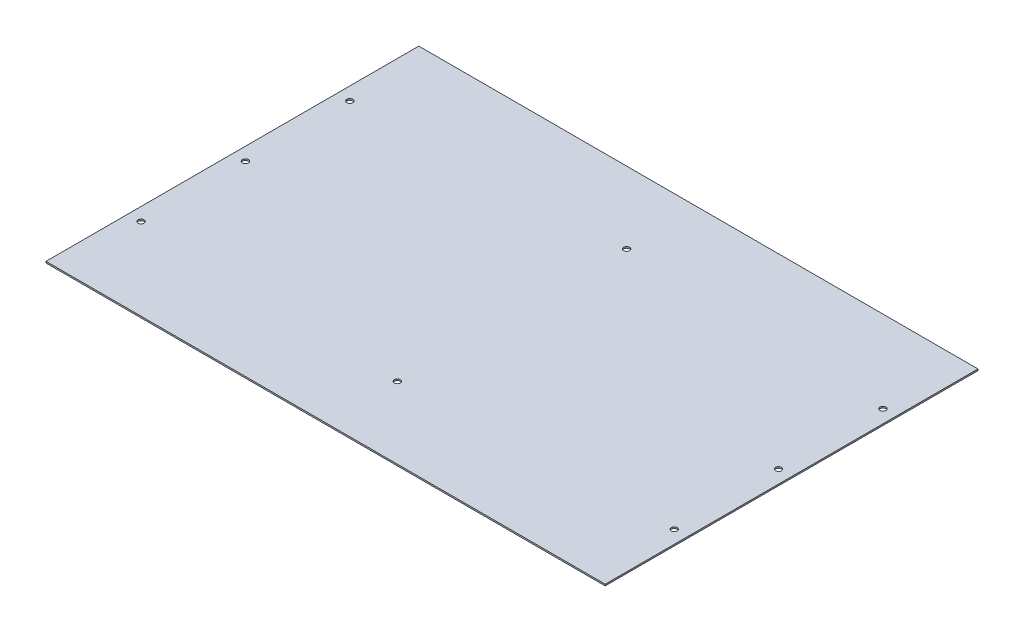
SolidWorks part; units mm, degrees
ref_plane "Front Plane" through (0, 0, 0) normal (0, 0, 1) x (1, 0, 0)
ref_plane "Top Plane" through (0, 0, 0) normal (0, 1, 0) x (1, 0, 0)
ref_plane "Right Plane" through (0, 0, 0) normal (1, 0, 0) x (0, 0, -1)
sketch "Sketch1" plane through (0, 0, 0) normal (0, 1, 0) x (1, 0, 0)
  line L1 (-375, 250) -> (375, 250)
  line L2 (-375, 250) -> (-375, -250)
  line L3 (-375, -250) -> (375, -250)
  line L4 (375, 250) -> (375, -250)
  line L5 (-375, 250) -> (375, -250) construction
  line L6 (-375, -250) -> (375, 250) construction
  point P0 (0, 0)
  dimension "D1" = 500
  dimension "D2" = 750
extrude "Boss-Extrude1" add sketch "Sketch1" along normal blind 2
sketch "Sketch2" plane through (0, 2, 0) normal (0, 1, 0) x (1, 0, 0)
  line L0 (-375, 250) -> (-375, -250) construction
  circle A0 centre (-357.5, 0) radius 4
  circle A1 centre (-357.5, 140) radius 4
  circle A2 centre (-357.5, -140) radius 4
  dimension "D1" = 8
  dimension "D3" = 8
  dimension "D4" = 8
  dimension "D2" = 17.5
  dimension "D5" = 140
  dimension "D6" = 140
extrude "Cut-Extrude1" cut sketch "Sketch2" against normal blind 2
mirror "Mirror1" about plane through (0, 0, 0) normal (1, 0, 0) of "Cut-Extrude1"
sketch "Sketch3" plane through (0, 2, 0) normal (0, 1, 0) x (1, 0, 0)
  line L0 (0, -1.1) -> (0, 1.1) construction
  line L1 (-1.1, 0) -> (1.1, 0) construction
  circle A0 centre (0, 153.75) radius 4
  circle A1 centre (0, -153.75) radius 4
  dimension "D1" = 8
  dimension "D4" = 8
  dimension "D2" = 153.75
  dimension "D3" = 153.75
extrude "Cut-Extrude2" cut sketch "Sketch3" against normal blind 2
